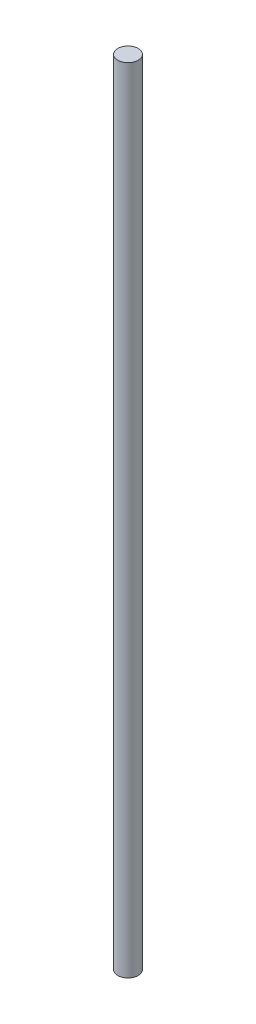
SolidWorks part; units mm, degrees
ref_plane "Front Plane" through (0, 0, 0) normal (0, 0, 1) x (1, 0, 0)
ref_plane "Top Plane" through (0, 0, 0) normal (0, 1, 0) x (1, 0, 0)
ref_plane "Right Plane" through (0, 0, 0) normal (1, 0, 0) x (0, 0, -1)
sketch "Sketch1" plane through (0, 0, 0) normal (0, 1, 0) x (1, 0, 0)
  circle A0 centre (0, 0) radius 4
extrude "Boss-Extrude1" add sketch "Sketch1" along normal blind 310
